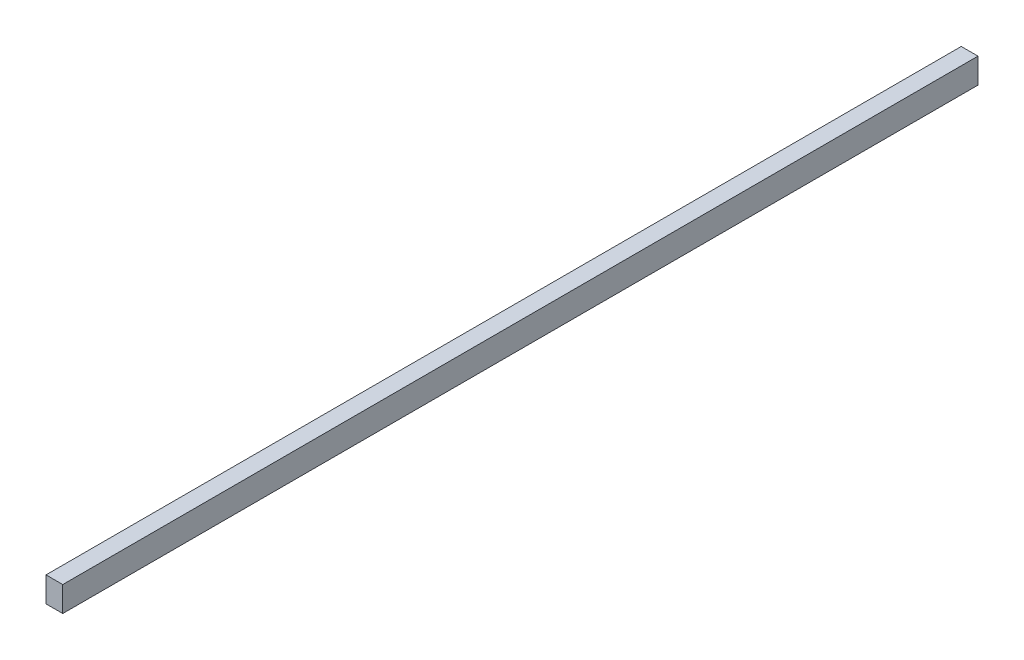
SolidWorks part; units mm, degrees
ref_plane "Plan de face" through (0, 0, 0) normal (0, 0, 1) x (1, 0, 0)
ref_plane "Plan de dessus" through (0, 0, 0) normal (0, 1, 0) x (1, 0, 0)
ref_plane "Plan de droite" through (0, 0, 0) normal (1, 0, 0) x (0, 0, -1)
sketch "Esquisse2" plane through (0, -21.5, 0) normal (0, 1, 0) x (1, 0, 0)
  line L0 (-261, -781) -> (-261, -759) construction
  line L1 (-261, -1093) -> (-241, -1093)
  line L2 (-261, -1093) -> (-261, 0)
  line L3 (-261, 0) -> (-241, 0)
  line L4 (-241, -1093) -> (-241, 0)
  line L5 (201, 0) -> (-261, 0) construction
  dimension "D1" = 20
extrude "Boss.-Extru.1" add sketch "Esquisse2" along normal up to surface (30 mm away)
